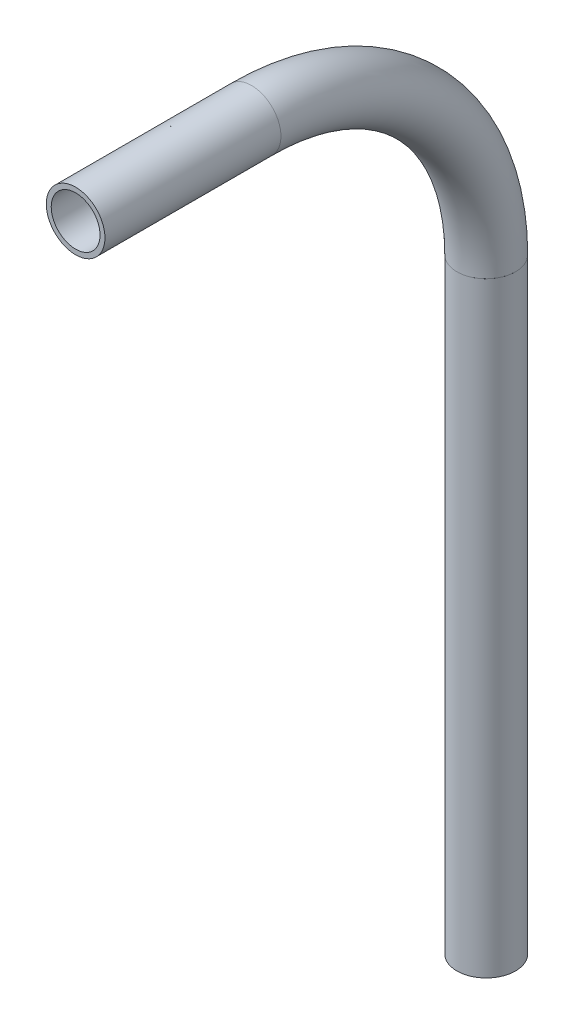
SolidWorks part; units mm, degrees
ref_plane "Front Plane" through (0, 0, 0) normal (0, 0, 1) x (1, 0, 0)
ref_plane "Top Plane" through (0, 0, 0) normal (0, 1, 0) x (1, 0, 0)
ref_plane "Right Plane" through (0, 0, 0) normal (1, 0, 0) x (0, 0, -1)
sketch "Sketch1" plane through (0, 0, 0) normal (1, 0, 0) x (0, 0, -1)
  line L0 (-296.5805, 1022.919) -> (-296.5805, 1154.0198)
  line L1 (-385.4805, 1204.8198) -> (-347.3805, 1204.8198)
  arc A0 (-296.5805, 1154.0198) -> (-347.3805, 1204.8198) centre (-347.3805, 1154.0198) ccw
  dimension "D1" = 50.8
  dimension "D2" = 38.1
other "Pipe 0.5 SCH 40(1)"
ref_plane "Plane1" through (0, 1022.919, 296.5805) normal (0, 1, 0) x (0, 0, 1)
sketch "Sketch11" plane through (0, 1022.919, 296.5805) normal (0, 1, 0) x (0, 0, 1)
  circle A0 centre (0, 0) radius 5.2832
  circle A1 centre (0, 0) radius 6.35
  point P5 (0, 0)
  dimension "In_dia" = 10.5664
  dimension "Out_dia" = 12.7
